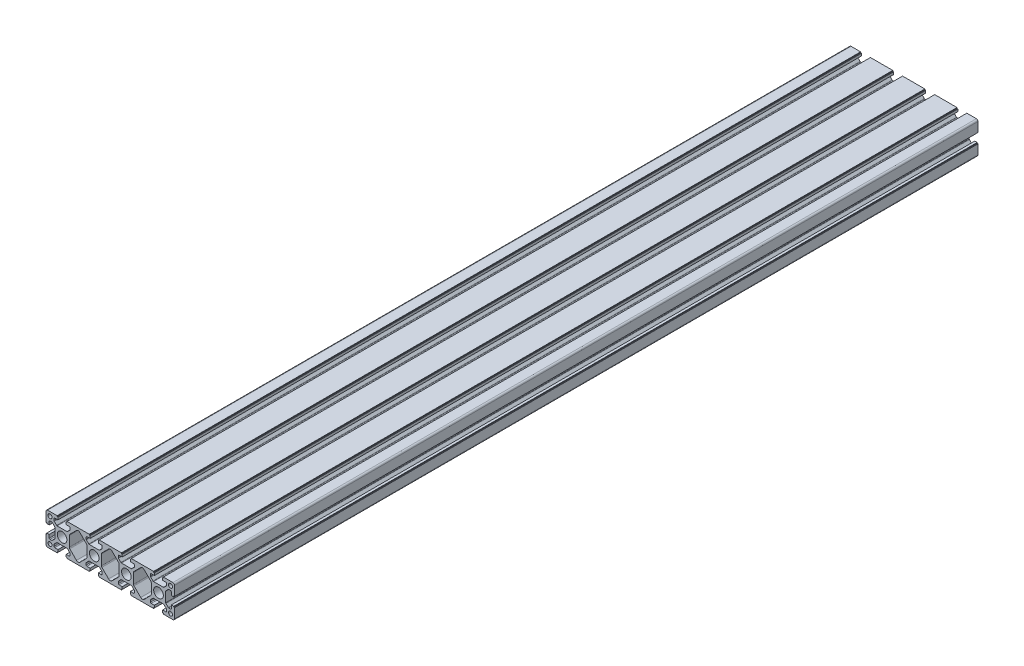
SolidWorks part; units mm, degrees
ref_plane "前视基准面" through (0, 0, 0) normal (0, 0, 1) x (1, 0, 0)
ref_plane "上视基准面" through (0, 0, 0) normal (0, 1, 0) x (1, 0, 0)
ref_plane "右视基准面" through (0, 0, 0) normal (1, 0, 0) x (0, 0, -1)
sketch "草图1" plane through (0, 0, 0) normal (0, 0, 1) x (1, 0, 0)
  line L0 (52.0665, 53.1169) -> (43.7736, 61.4098)
  line L1 (52.6522, 38.8951) -> (52.6522, 51.7027)
  line L2 (43.7736, 29.188) -> (52.0665, 37.4809)
  line L3 (31.238, 37.4809) -> (39.5309, 29.188)
  line L4 (30.6522, 51.7027) -> (30.6522, 38.8951)
  line L5 (39.5309, 61.4098) -> (31.238, 53.1169)
  line L6 (123.7736, 29.188) -> (132.0665, 37.4809)
  line L7 (111.238, 37.4809) -> (119.5309, 29.188)
  line L8 (110.6522, 51.7027) -> (110.6522, 38.8951)
  line L9 (119.5309, 61.4098) -> (111.238, 53.1169)
  line L10 (132.0665, 53.1169) -> (123.7736, 61.4098)
  line L11 (132.6522, 38.8951) -> (132.6522, 51.7027)
  line L12 (83.7736, 29.188) -> (92.0665, 37.4809)
  line L13 (71.238, 37.4809) -> (79.5309, 29.188)
  line L14 (70.6522, 51.7027) -> (70.6522, 38.8951)
  line L15 (79.5309, 61.4098) -> (71.238, 53.1169)
  line L16 (92.0665, 53.1169) -> (83.7736, 61.4098)
  line L17 (92.6522, 38.8951) -> (92.6522, 51.7027)
  line L18 (67.7522, 25.2989) -> (67.7522, 26.2989)
  line L19 (95.5522, 25.2989) -> (67.7522, 25.2989)
  line L20 (95.5522, 26.2989) -> (95.5522, 25.2989)
  line L21 (96.5522, 26.2989) -> (95.5522, 26.2989)
  line L22 (96.5522, 29.2989) -> (96.5522, 26.2989)
  line L23 (92.6522, 29.2989) -> (96.5522, 29.2989)
  line L24 (91.6522, 32.4098) -> (91.6522, 30.2989)
  line L25 (94.8342, 36.006) -> (91.9451, 33.1169)
  line L26 (107.7632, 36.2989) -> (95.5413, 36.2989)
  line L27 (111.3593, 33.1169) -> (108.4703, 36.006)
  line L28 (111.6522, 30.2989) -> (111.6522, 32.4098)
  line L29 (106.7522, 29.2989) -> (110.6522, 29.2989)
  line L30 (106.7522, 26.2989) -> (106.7522, 29.2989)
  line L31 (107.7522, 26.2989) -> (106.7522, 26.2989)
  line L32 (107.7522, 25.2989) -> (107.7522, 26.2989)
  line L33 (135.5522, 25.2989) -> (107.7522, 25.2989)
  line L34 (135.5522, 26.2989) -> (135.5522, 25.2989)
  line L35 (136.5522, 26.2989) -> (135.5522, 26.2989)
  line L36 (136.5522, 29.2989) -> (136.5522, 26.2989)
  line L37 (132.6522, 29.2989) -> (136.5522, 29.2989)
  line L38 (131.6522, 32.4098) -> (131.6522, 30.2989)
  line L39 (134.8342, 36.006) -> (131.9451, 33.1169)
  line L40 (147.7632, 36.2989) -> (135.5413, 36.2989)
  line L41 (151.3593, 33.1169) -> (148.4703, 36.006)
  line L42 (151.6522, 30.2989) -> (151.6522, 32.4098)
  line L43 (146.7522, 29.2989) -> (150.6522, 29.2989)
  line L44 (146.7522, 26.2989) -> (146.7522, 29.2989)
  line L45 (147.7522, 26.2989) -> (146.7522, 26.2989)
  line L46 (147.7522, 25.2989) -> (147.7522, 26.2989)
  line L47 (159.6522, 25.2989) -> (147.7522, 25.2989)
  line L48 (161.6522, 39.1989) -> (161.6522, 27.2989)
  line L49 (160.6522, 39.1989) -> (161.6522, 39.1989)
  line L50 (160.6522, 40.1989) -> (160.6522, 39.1989)
  line L51 (157.6522, 40.1989) -> (160.6522, 40.1989)
  line L52 (157.6522, 36.2989) -> (157.6522, 40.1989)
  line L53 (154.5413, 35.2989) -> (156.6522, 35.2989)
  line L54 (150.9451, 38.4809) -> (153.8342, 35.5918)
  line L55 (150.6522, 51.4098) -> (150.6522, 39.188)
  line L56 (153.8342, 55.006) -> (150.9451, 52.1169)
  line L57 (156.6522, 55.2989) -> (154.5413, 55.2989)
  line L58 (157.6522, 50.3989) -> (157.6522, 54.2989)
  line L59 (160.6522, 50.3989) -> (157.6522, 50.3989)
  line L60 (160.6522, 51.3989) -> (160.6522, 50.3989)
  line L61 (161.6522, 51.3989) -> (160.6522, 51.3989)
  line L62 (161.6522, 63.2989) -> (161.6522, 51.3989)
  line L63 (147.7522, 65.2989) -> (159.6522, 65.2989)
  line L64 (147.7522, 64.2989) -> (147.7522, 65.2989)
  line L65 (146.7522, 64.2989) -> (147.7522, 64.2989)
  line L66 (146.7522, 61.2989) -> (146.7522, 64.2989)
  line L67 (150.6522, 61.2989) -> (146.7522, 61.2989)
  line L68 (151.6522, 58.188) -> (151.6522, 60.2989)
  line L69 (148.4703, 54.5918) -> (151.3593, 57.4809)
  line L70 (135.5413, 54.2989) -> (147.7632, 54.2989)
  line L71 (131.9451, 57.4809) -> (134.8342, 54.5918)
  line L72 (131.6522, 60.2989) -> (131.6522, 58.188)
  line L73 (136.5522, 61.2989) -> (132.6522, 61.2989)
  line L74 (136.5522, 64.2989) -> (136.5522, 61.2989)
  line L75 (135.5522, 64.2989) -> (136.5522, 64.2989)
  line L76 (135.5522, 65.2989) -> (135.5522, 64.2989)
  line L77 (107.7522, 65.2989) -> (135.5522, 65.2989)
  line L78 (107.7522, 64.2989) -> (107.7522, 65.2989)
  line L79 (106.7522, 64.2989) -> (107.7522, 64.2989)
  line L80 (106.7522, 61.2989) -> (106.7522, 64.2989)
  line L81 (110.6522, 61.2989) -> (106.7522, 61.2989)
  line L82 (111.6522, 58.188) -> (111.6522, 60.2989)
  line L83 (108.4703, 54.5918) -> (111.3593, 57.4809)
  line L84 (95.5413, 54.2989) -> (107.7632, 54.2989)
  line L85 (91.9451, 57.4809) -> (94.8342, 54.5918)
  line L86 (91.6522, 60.2989) -> (91.6522, 58.188)
  line L87 (96.5522, 61.2989) -> (92.6522, 61.2989)
  line L88 (96.5522, 64.2989) -> (96.5522, 61.2989)
  line L89 (95.5522, 64.2989) -> (96.5522, 64.2989)
  line L90 (95.5522, 65.2989) -> (95.5522, 64.2989)
  line L91 (67.7522, 65.2989) -> (95.5522, 65.2989)
  line L92 (67.7522, 64.2989) -> (67.7522, 65.2989)
  line L93 (66.7522, 64.2989) -> (67.7522, 64.2989)
  line L94 (66.7522, 61.2989) -> (66.7522, 64.2989)
  line L95 (70.6522, 61.2989) -> (66.7522, 61.2989)
  line L96 (71.6522, 58.188) -> (71.6522, 60.2989)
  line L97 (68.4703, 54.5918) -> (71.3593, 57.4809)
  line L98 (55.5413, 54.2989) -> (67.7632, 54.2989)
  line L99 (51.9451, 57.4809) -> (54.8342, 54.5918)
  line L100 (51.6522, 60.2989) -> (51.6522, 58.188)
  line L101 (56.5522, 61.2989) -> (52.6522, 61.2989)
  line L102 (56.5522, 64.2989) -> (56.5522, 61.2989)
  line L103 (55.5522, 64.2989) -> (56.5522, 64.2989)
  line L104 (55.5522, 65.2989) -> (55.5522, 64.2989)
  line L105 (27.7522, 65.2989) -> (55.5522, 65.2989)
  line L106 (27.7522, 64.2989) -> (27.7522, 65.2989)
  line L107 (26.7522, 64.2989) -> (27.7522, 64.2989)
  line L108 (26.7522, 61.2989) -> (26.7522, 64.2989)
  line L109 (30.6522, 61.2989) -> (26.7522, 61.2989)
  line L110 (31.6522, 58.188) -> (31.6522, 60.2989)
  line L111 (28.4703, 54.5918) -> (31.3593, 57.4809)
  line L112 (15.5413, 54.2989) -> (27.7632, 54.2989)
  line L113 (11.9451, 57.4809) -> (14.8342, 54.5918)
  line L114 (11.6522, 60.2989) -> (11.6522, 58.188)
  line L115 (16.5522, 61.2989) -> (12.6522, 61.2989)
  line L116 (16.5522, 64.2989) -> (16.5522, 61.2989)
  line L117 (15.5522, 64.2989) -> (16.5522, 64.2989)
  line L118 (15.5522, 65.2989) -> (15.5522, 64.2989)
  line L119 (3.6522, 65.2989) -> (15.5522, 65.2989)
  line L120 (1.6522, 51.3989) -> (1.6522, 63.2989)
  line L121 (2.6522, 51.3989) -> (1.6522, 51.3989)
  line L122 (2.6522, 50.3989) -> (2.6522, 51.3989)
  line L123 (5.6522, 50.3989) -> (2.6522, 50.3989)
  line L124 (5.6522, 54.2989) -> (5.6522, 50.3989)
  line L125 (8.7632, 55.2989) -> (6.6522, 55.2989)
  line L126 (12.3593, 52.1169) -> (9.4703, 55.006)
  line L127 (12.6522, 39.188) -> (12.6522, 51.4098)
  line L128 (9.4703, 35.5918) -> (12.3593, 38.4809)
  line L129 (6.6522, 35.2989) -> (8.7632, 35.2989)
  line L130 (5.6522, 40.1989) -> (5.6522, 36.2989)
  line L131 (2.6522, 40.1989) -> (5.6522, 40.1989)
  line L132 (2.6522, 39.1989) -> (2.6522, 40.1989)
  line L133 (1.6522, 39.1989) -> (2.6522, 39.1989)
  line L134 (1.6522, 27.2989) -> (1.6522, 39.1989)
  line L135 (15.5522, 25.2989) -> (3.6522, 25.2989)
  line L136 (15.5522, 26.2989) -> (15.5522, 25.2989)
  line L137 (16.5522, 26.2989) -> (15.5522, 26.2989)
  line L138 (16.5522, 29.2989) -> (16.5522, 26.2989)
  line L139 (12.6522, 29.2989) -> (16.5522, 29.2989)
  line L140 (11.6522, 32.4098) -> (11.6522, 30.2989)
  line L141 (14.8342, 36.006) -> (11.9451, 33.1169)
  line L142 (27.7632, 36.2989) -> (15.5413, 36.2989)
  line L143 (31.3593, 33.1169) -> (28.4703, 36.006)
  line L144 (31.6522, 30.2989) -> (31.6522, 32.4098)
  line L145 (26.7522, 29.2989) -> (30.6522, 29.2989)
  line L146 (26.7522, 26.2989) -> (26.7522, 29.2989)
  line L147 (27.7522, 26.2989) -> (26.7522, 26.2989)
  line L148 (27.7522, 25.2989) -> (27.7522, 26.2989)
  line L149 (55.5522, 25.2989) -> (27.7522, 25.2989)
  line L150 (55.5522, 26.2989) -> (55.5522, 25.2989)
  line L151 (56.5522, 26.2989) -> (55.5522, 26.2989)
  line L152 (56.5522, 29.2989) -> (56.5522, 26.2989)
  line L153 (52.6522, 29.2989) -> (56.5522, 29.2989)
  line L154 (51.6522, 32.4098) -> (51.6522, 30.2989)
  line L155 (54.8342, 36.006) -> (51.9451, 33.1169)
  line L156 (67.7632, 36.2989) -> (55.5413, 36.2989)
  line L157 (71.3593, 33.1169) -> (68.4703, 36.006)
  line L158 (71.6522, 30.2989) -> (71.6522, 32.4098)
  line L159 (66.7522, 29.2989) -> (70.6522, 29.2989)
  line L160 (66.7522, 26.2989) -> (66.7522, 29.2989)
  line L161 (67.7522, 26.2989) -> (66.7522, 26.2989)
  arc A0 (52.6522, 51.7027) -> (52.0665, 53.1169) centre (50.6522, 51.7027) ccw
  arc A1 (52.0665, 37.4809) -> (52.6522, 38.8951) centre (50.6522, 38.8951) ccw
  arc A2 (39.5309, 29.188) -> (43.7736, 29.188) centre (41.6522, 31.3093) ccw
  arc A3 (30.6522, 38.8951) -> (31.238, 37.4809) centre (32.6522, 38.8951) ccw
  arc A4 (31.238, 53.1169) -> (30.6522, 51.7027) centre (32.6522, 51.7027) ccw
  arc A5 (132.0665, 37.4809) -> (132.6522, 38.8951) centre (130.6522, 38.8951) ccw
  arc A6 (119.5309, 29.188) -> (123.7736, 29.188) centre (121.6522, 31.3093) ccw
  arc A7 (110.6522, 38.8951) -> (111.238, 37.4809) centre (112.6522, 38.8951) ccw
  arc A8 (111.238, 53.1169) -> (110.6522, 51.7027) centre (112.6522, 51.7027) ccw
  arc A9 (123.7736, 61.4098) -> (119.5309, 61.4098) centre (121.6522, 59.2885) ccw
  arc A10 (132.6522, 51.7027) -> (132.0665, 53.1169) centre (130.6522, 51.7027) ccw
  arc A11 (92.0665, 37.4809) -> (92.6522, 38.8951) centre (90.6522, 38.8951) ccw
  arc A12 (79.5309, 29.188) -> (83.7736, 29.188) centre (81.6522, 31.3093) ccw
  arc A13 (70.6522, 38.8951) -> (71.238, 37.4809) centre (72.6522, 38.8951) ccw
  arc A14 (71.238, 53.1169) -> (70.6522, 51.7027) centre (72.6522, 51.7027) ccw
  arc A15 (83.7736, 61.4098) -> (79.5309, 61.4098) centre (81.6522, 59.2885) ccw
  arc A16 (92.6522, 51.7027) -> (92.0665, 53.1169) centre (90.6522, 51.7027) ccw
  arc A17 (91.6522, 30.2989) -> (92.6522, 29.2989) centre (92.6522, 30.2989) ccw
  arc A18 (91.9451, 33.1169) -> (91.6522, 32.4098) centre (92.6522, 32.4098) ccw
  arc A19 (95.5413, 36.2989) -> (94.8342, 36.006) centre (95.5413, 35.2989) ccw
  arc A20 (108.4703, 36.006) -> (107.7632, 36.2989) centre (107.7632, 35.2989) ccw
  arc A21 (111.6522, 32.4098) -> (111.3593, 33.1169) centre (110.6522, 32.4098) ccw
  arc A22 (110.6522, 29.2989) -> (111.6522, 30.2989) centre (110.6522, 30.2989) ccw
  arc A23 (131.6522, 30.2989) -> (132.6522, 29.2989) centre (132.6522, 30.2989) ccw
  arc A24 (131.9451, 33.1169) -> (131.6522, 32.4098) centre (132.6522, 32.4098) ccw
  arc A25 (135.5413, 36.2989) -> (134.8342, 36.006) centre (135.5413, 35.2989) ccw
  arc A26 (148.4703, 36.006) -> (147.7632, 36.2989) centre (147.7632, 35.2989) ccw
  arc A27 (151.6522, 32.4098) -> (151.3593, 33.1169) centre (150.6522, 32.4098) ccw
  arc A28 (150.6522, 29.2989) -> (151.6522, 30.2989) centre (150.6522, 30.2989) ccw
  arc A29 (159.6522, 25.2989) -> (161.6522, 27.2989) centre (159.6522, 27.2989) ccw
  arc A30 (156.6522, 35.2989) -> (157.6522, 36.2989) centre (156.6522, 36.2989) ccw
  arc A31 (153.8342, 35.5918) -> (154.5413, 35.2989) centre (154.5413, 36.2989) ccw
  arc A32 (150.6522, 39.188) -> (150.9451, 38.4809) centre (151.6522, 39.188) ccw
  arc A33 (150.9451, 52.1169) -> (150.6522, 51.4098) centre (151.6522, 51.4098) ccw
  arc A34 (154.5413, 55.2989) -> (153.8342, 55.006) centre (154.5413, 54.2989) ccw
  arc A35 (157.6522, 54.2989) -> (156.6522, 55.2989) centre (156.6522, 54.2989) ccw
  arc A36 (161.6522, 63.2989) -> (159.6522, 65.2989) centre (159.6522, 63.2989) ccw
  arc A37 (151.6522, 60.2989) -> (150.6522, 61.2989) centre (150.6522, 60.2989) ccw
  arc A38 (151.3593, 57.4809) -> (151.6522, 58.188) centre (150.6522, 58.188) ccw
  arc A39 (147.7632, 54.2989) -> (148.4703, 54.5918) centre (147.7632, 55.2989) ccw
  arc A40 (134.8342, 54.5918) -> (135.5413, 54.2989) centre (135.5413, 55.2989) ccw
  arc A41 (131.6522, 58.188) -> (131.9451, 57.4809) centre (132.6522, 58.188) ccw
  arc A42 (132.6522, 61.2989) -> (131.6522, 60.2989) centre (132.6522, 60.2989) ccw
  arc A43 (111.6522, 60.2989) -> (110.6522, 61.2989) centre (110.6522, 60.2989) ccw
  arc A44 (111.3593, 57.4809) -> (111.6522, 58.188) centre (110.6522, 58.188) ccw
  arc A45 (107.7632, 54.2989) -> (108.4703, 54.5918) centre (107.7632, 55.2989) ccw
  arc A46 (94.8342, 54.5918) -> (95.5413, 54.2989) centre (95.5413, 55.2989) ccw
  arc A47 (91.6522, 58.188) -> (91.9451, 57.4809) centre (92.6522, 58.188) ccw
  arc A48 (92.6522, 61.2989) -> (91.6522, 60.2989) centre (92.6522, 60.2989) ccw
  arc A49 (71.6522, 60.2989) -> (70.6522, 61.2989) centre (70.6522, 60.2989) ccw
  arc A50 (71.3593, 57.4809) -> (71.6522, 58.188) centre (70.6522, 58.188) ccw
  arc A51 (67.7632, 54.2989) -> (68.4703, 54.5918) centre (67.7632, 55.2989) ccw
  arc A52 (54.8342, 54.5918) -> (55.5413, 54.2989) centre (55.5413, 55.2989) ccw
  arc A53 (51.6522, 58.188) -> (51.9451, 57.4809) centre (52.6522, 58.188) ccw
  arc A54 (52.6522, 61.2989) -> (51.6522, 60.2989) centre (52.6522, 60.2989) ccw
  arc A55 (31.6522, 60.2989) -> (30.6522, 61.2989) centre (30.6522, 60.2989) ccw
  arc A56 (31.3593, 57.4809) -> (31.6522, 58.188) centre (30.6522, 58.188) ccw
  arc A57 (27.7632, 54.2989) -> (28.4703, 54.5918) centre (27.7632, 55.2989) ccw
  arc A58 (14.8342, 54.5918) -> (15.5413, 54.2989) centre (15.5413, 55.2989) ccw
  arc A59 (11.6522, 58.188) -> (11.9451, 57.4809) centre (12.6522, 58.188) ccw
  arc A60 (12.6522, 61.2989) -> (11.6522, 60.2989) centre (12.6522, 60.2989) ccw
  arc A61 (3.6522, 65.2989) -> (1.6522, 63.2989) centre (3.6522, 63.2989) ccw
  arc A62 (6.6522, 55.2989) -> (5.6522, 54.2989) centre (6.6522, 54.2989) ccw
  arc A63 (9.4703, 55.006) -> (8.7632, 55.2989) centre (8.7632, 54.2989) ccw
  arc A64 (12.6522, 51.4098) -> (12.3593, 52.1169) centre (11.6522, 51.4098) ccw
  arc A65 (12.3593, 38.4809) -> (12.6522, 39.188) centre (11.6522, 39.188) ccw
  arc A66 (8.7632, 35.2989) -> (9.4703, 35.5918) centre (8.7632, 36.2989) ccw
  arc A67 (5.6522, 36.2989) -> (6.6522, 35.2989) centre (6.6522, 36.2989) ccw
  arc A68 (1.6522, 27.2989) -> (3.6522, 25.2989) centre (3.6522, 27.2989) ccw
  arc A69 (11.6522, 30.2989) -> (12.6522, 29.2989) centre (12.6522, 30.2989) ccw
  arc A70 (11.9451, 33.1169) -> (11.6522, 32.4098) centre (12.6522, 32.4098) ccw
  arc A71 (15.5413, 36.2989) -> (14.8342, 36.006) centre (15.5413, 35.2989) ccw
  arc A72 (28.4703, 36.006) -> (27.7632, 36.2989) centre (27.7632, 35.2989) ccw
  arc A73 (31.6522, 32.4098) -> (31.3593, 33.1169) centre (30.6522, 32.4098) ccw
  arc A74 (30.6522, 29.2989) -> (31.6522, 30.2989) centre (30.6522, 30.2989) ccw
  arc A75 (51.6522, 30.2989) -> (52.6522, 29.2989) centre (52.6522, 30.2989) ccw
  arc A76 (51.9451, 33.1169) -> (51.6522, 32.4098) centre (52.6522, 32.4098) ccw
  arc A77 (55.5413, 36.2989) -> (54.8342, 36.006) centre (55.5413, 35.2989) ccw
  arc A78 (68.4703, 36.006) -> (67.7632, 36.2989) centre (67.7632, 35.2989) ccw
  arc A79 (71.6522, 32.4098) -> (71.3593, 33.1169) centre (70.6522, 32.4098) ccw
  arc A80 (70.6522, 29.2989) -> (71.6522, 30.2989) centre (70.6522, 30.2989) ccw
  circle A81 centre (6.6522, 60.2989) radius 2.5
  circle A82 centre (6.6522, 30.2989) radius 2.5
  circle A83 centre (21.6522, 45.2989) radius 6
  circle A84 centre (61.6522, 45.2989) radius 6
  circle A85 centre (101.6522, 45.2989) radius 6
  circle A86 centre (141.6522, 45.2989) radius 6
  circle A87 centre (156.6522, 30.2989) radius 2.5
  circle A88 centre (156.6522, 60.2989) radius 2.5
  arc A89 (43.7736, 61.4098) -> (39.5309, 61.4098) centre (41.6522, 59.2885) ccw
extrude "拉伸1" add sketch "草图1" along normal blind 1000
